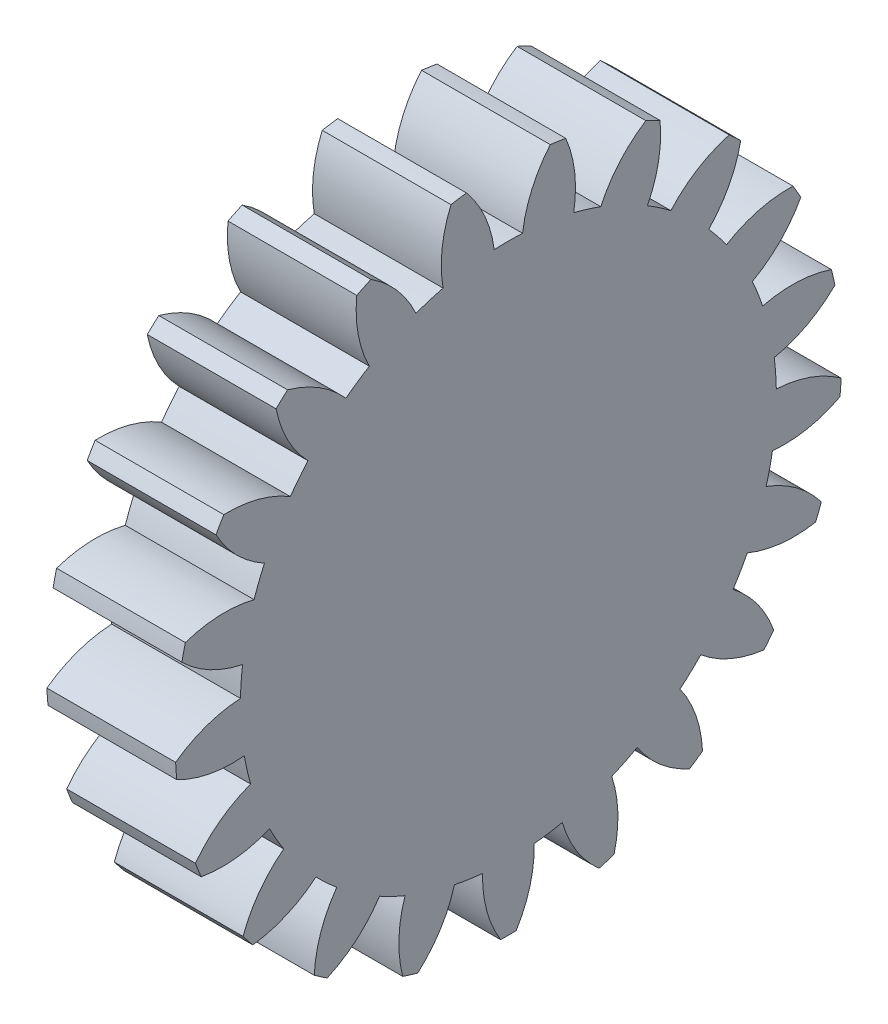
SolidWorks part; units mm, degrees
ref_plane "Plane1" through (0, 0, 0) normal (0, 0, 1) x (1, 0, 0)
ref_plane "Plane2" through (0, 0, 0) normal (0, 1, 0) x (1, 0, 0)
ref_plane "Plane3" through (0, 0, 0) normal (1, 0, 0) x (0, 0, -1)
sketch "HoldingSke" plane through (0, 0, 0) normal (0, 1, 0) x (1, 0, 0)
  line L0 (0, 0) -> (0.4149, -0.1593)
  line L1 (-15, 0) -> (100, 0) construction
  line L2 (0, 0) -> (-2.1039, 2.3779)
  line L3 (0, 0) -> (-11.863, 4.5341)
  line L4 (0, 0) -> (8.0624, 3.0949)
  line L5 (0, 0) -> (-46.8476, -17.4728)
  line L6 (0, 0) -> (-8.2896, -5.593)
  line L7 (-2.1039, 2.3779) -> (8.6586, 51.2059)
  line L8 (-76.2, 54.61) -> (-72.9, 54.61)
  line L9 (-71.009, 38.7566) -> (-53.1078, 45.2721)
  line L10 (-76.2, 71.12) -> (104.1128, 71.12)
  line L11 (0, 0) -> (-10, 0)
  line L12 (-76.2, 101.6) -> (-76.123, 101.6)
  line L13 (24.9733, 27.94) -> (52.9518, 28.4284)
  line L14 (24.9733, 27.94) -> (24.9743, 27.94)
  line L15 (24.9733, 27.94) -> (100.4006, 29.5858)
  line L16 (-63.627, -2.25) -> (-12.827, -2.25)
  circle A0 centre (0, 0) radius 11
  circle A1 centre (0, 0) radius 20.8115
  circle A2 centre (0, 0) radius 37.5
  circle A3 centre (0, 0) radius 11
  dimension "MHD" = 41.623
  dimension "Hub_dia" = 75
  dimension "Bore" = 22
  dimension "MBD" = 22
  dimension "Num_teeth" = 21
  dimension "Pitch" = 0.4444
  dimension "Overall_len" = 50
  dimension "Show_teeth" = 21
  dimension "Thickness" = 10
  dimension "OAL" = 50.0001
  dimension "T_dim" = 3.3
  dimension "Ap" = 20
  dimension "H" = 19.05
  dimension "Pitch_radius" = 180.3128
  dimension "Width" = 10
  dimension "Backlash" = 0.077
  dimension "Addendum_fac" = 1
  dimension "Dedendum_fac" = 1.25
  dimension "Clearance_fac" = 0.25
  dimension "Dedendum_add" = 0.001
  dimension "Module" = 2.25
sketch "BasProSke" plane through (0, 0, 0) normal (0, 1, 0) x (1, 0, 0)
  line L0 (-10, 0) -> (60, 0) construction
  line L1 (0, 0) -> (0, 25.875)
  line L2 (0, 0) -> (10, 0)
  line L3 (10, 0) -> (10, 25.875)
  line L4 (10, 25.875) -> (0, 25.875)
  dimension "Thickness" = 10
  dimension "Diameter" = 51.75
revolve "Base-Revolve" add sketch "BasProSke" angle 360 about L0
sketch "TooCutSke" plane through (0, 0, 0) normal (1, 0, 0) x (0, 0, -1)
  line L1 (0, 0) -> (0, 107) construction
  line L2 (0, 0) -> (-1.9002, 23.5485) construction
  line L3 (0, 0) -> (-7.0255, 46.6108) construction
  line L4 (-1.9002, 23.5485) -> (-3.5127, 23.3054) construction
  arc A0 (1.1014, 20.7823) -> (-1.1014, 20.7823) centre (0, 0) ccw
  arc A1 (3.2722, 25.6929) -> (-3.2722, 25.6929) centre (0, 0) ccw
  circle A2 centre (0, 0) radius 23.625 construction
  circle A3 centre (0, 0) radius 22.2002 construction
  arc A4 (-1.1014, 20.7823) -> (-3.2722, 25.6929) centre (-10.4739, 19.5742) ccw
  arc A5 (3.2722, 25.6929) -> (1.1014, 20.7823) centre (10.4739, 19.5742) ccw
  dimension "Root_dia" = 41.623
  dimension "Overcut_dia" = 51.8008
  dimension "Pitch_dia" = 47.25
  dimension "Base_dia" = 44.4005
  dimension "Flank_rad" = 9.45
  dimension "Half_ang" = 8.571
  dimension "Half_CT" = 1.6307
extrude "ToothCut" cut sketch "TooCutSke" along normal through all
fillet "Breaks" [suppressed] radius 0.045
fillet "RootFillets" [suppressed] radius 0.5635
pattern_circular "TeethCuts" count 21 every 17.143 about axis through (-10, 0, 0) along (1, 0, 0) of "ToothCut", "RootFillets", "Breaks"
sketch "HubNeaOneSke" plane through (0, 0, 0) normal (-1, 0, 0) x (0, 0, 1)
  circle A0 centre (0, 0) radius 20.8115
  dimension "Diameter" = 41.623
extrude "HubNearOne" [suppressed] add sketch "HubNeaOneSke" along normal blind 40.0001
sketch "HubNeaBotSke" plane through (0, 0, 0) normal (-1, 0, 0) x (0, 0, 1)
  circle A0 centre (0, 0) radius 20.8115
  dimension "Diameter" = 41.623
extrude "HubNearBoth" [suppressed] add sketch "HubNeaBotSke" along normal blind 20
ref_plane "FarPln" through (10, 0, 0) normal (1, 0, 0) x (0, 0, -1)
sketch "HubFarSke" plane through (10, 0, 0) normal (1, 0, 0) x (0, 0, -1)
  circle A0 centre (0, 0) radius 20.8115
  dimension "Diameter" = 41.623
extrude "HubFar" [suppressed] add sketch "HubFarSke" along normal blind 20
sketch "BorSke" plane through (0, 0, 0) normal (1, 0, 0) x (0, 0, -1)
  circle A0 centre (0, 0) radius 11
  dimension "Diameter" = 22
extrude "Bore" cut sketch "BorSke" along normal mid plane 100.0001
sketch "KeySke" plane through (0, 0, 0) normal (1, 0, 0) x (0, 0, -1)
  line L0 (-4, 0) -> (-4, 14.3)
  line L1 (-4, 14.3) -> (4, 14.3)
  line L2 (4, 14.3) -> (4, 0)
  line L3 (0, 0) -> (0, 34) construction
  line L4 (-4, 0) -> (4, 0)
  dimension "Offset" = 14.3
  dimension "Width" = 8
extrude "Keyway" [suppressed] cut sketch "KeySke" along normal mid plane 100.0001
pattern_circular "Keyway2" [suppressed] count 2 every 90 about axis through (-10, 0, 0) along (1, 0, 0)
sketch "Sketch1" plane through (10, 0, 0) normal (1, 0, 0) x (0, 0, -1)
  circle A0 centre (0, 0) radius 11 construction
  circle A1 centre (0, 0) radius 11
sketch "Sketch2" plane through (10, 0, 0) normal (1, 0, 0) x (0, 0, -1)
  circle A0 centre (0, 0) radius 11 construction
  circle A1 centre (0, 0) radius 11
extrude "Boss-Extrude2" add sketch "Sketch2" against normal blind 3
equation "' \"Module@HoldingSke\" = 6.35"
equation "' \"Num_teeth@HoldingSke\" = 12"
equation "' \"Ap@HoldingSke\" =  20"
equation "' \"Ap@HoldingSke\" = 20"
equation "' \"Width@HoldingSke\" = 0.5 * 25.4"
equation "' \"Hub_dia@HoldingSke\"= 1 * 25.4"
equation "' \"Hub_dia@HoldingSke\" = 1 * 25.4"
equation "' \"Overall_len@HoldingSke\" = 1.0 * 25.4"
equation "' \"Bore@HoldingSke\" = 0.75 * 25.4"
equation "' \"T_dim@HoldingSke\" = 0.1 * 25.4"
equation "' \"Width@KeySke\" = 0.25 * 25.4"
equation "' \"Show_teeth@HoldingSke\" = 13"
equation "' \"Backlash@HoldingSke\" = 0.009 * 25.4"
equation "' \"Addendum_fac@HoldingSke\" = 1.0"
equation "' \"Dedendum_fac@HoldingSke\" = 1.25"
equation "' \"Dedendum_add@HoldingSke\" = 0.00005 * 25.4"
equation "' \"Clearance_fac@HoldingSke\" = 0.25"
equation "\"Pitch@HoldingSke\" = 1 / \"Module@HoldingSke\""
equation "\"Overcut_dia@TooCutSke\" = (\"Num_teeth@HoldingSke\" + 2 * \"Addendum_fac@HoldingSke\") / \"Pitch@HoldingSke\" + 0.002 * 25.4"
equation "\"Pitch_dia@TooCutSke\" = \"Num_teeth@HoldingSke\" / \"Pitch@HoldingSke\""
equation "\"Base_dia@TooCutSke\" = \"Num_teeth@HoldingSke\" / \"Pitch@HoldingSke\" * cos((\"Ap@HoldingSke\"  * 3.14159265 / 180))"
equation "\"Root_dia@TooCutSke\" = (\"Num_teeth@HoldingSke\" + 2) / \"Pitch@HoldingSke\" - 2 * (\"Addendum_fac@HoldingSke\" + \"Dedendum_fac@HoldingSke\") / \"Pitch@HoldingSke\" - \"Dedendum_add@HoldingSke\" * 2"
equation "\"Half_ang@TooCutSke\" = 180 / \"Num_teeth@HoldingSke\""
equation "\"Half_CT@TooCutSke\" = \"Num_teeth@HoldingSke\" / \"Pitch@HoldingSke\" * sin((3.14159265 / 2 / \"Num_teeth@HoldingSke\")) / 2 - 7 * \"Backlash@HoldingSke\" / 4"
equation "\"Flank_rad@TooCutSke\" = \"Num_teeth@HoldingSke\" / \"Pitch@HoldingSke\" / 5"
equation "\"Radius@RootFillets\" = \"Clearance_fac@HoldingSke\" / \"Pitch@HoldingSke\" + \"Dedendum_add@HoldingSke\""
equation "\"Break_rad@Breaks\" = 0.02 / \"Pitch@HoldingSke\""
equation "\"Thickness@HoldingSke\" = \"Width@HoldingSke\""
equation "\"OAL@HoldingSke\" = \"Thickness@HoldingSke\""
equation "\"MHD@HoldingSke\" = (\"Num_teeth@HoldingSke\" + 2) / \"Pitch@HoldingSke\" - 2 * (\"Addendum_fac@HoldingSke\" + \"Dedendum_fac@HoldingSke\")  / \"Pitch@HoldingSke\" - \"Dedendum_add@HoldingSke\" * 2"
equation "\"MBD@HoldingSke\" = (\"Num_teeth@HoldingSke\" + 2) / \"Pitch@HoldingSke\" - 2 * (\"Addendum_fac@HoldingSke\" + \"Dedendum_fac@HoldingSke\")  / \"Pitch@HoldingSke\" - \"Dedendum_add@HoldingSke\" * 2 - 0.002 * 25.4"
equation "\"MHD@HoldingSke\" = ((sgn( \"MHD@HoldingSke\" - \"Hub_dia@HoldingSke\" )-1)*( \"MHD@HoldingSke\" - \"Hub_dia@HoldingSke\" ))/-2+ \"Hub_dia@HoldingSke\""
equation "\"MBD@HoldingSke\" = ((sgn( \"MBD@HoldingSke\" - \"Bore@HoldingSke\" )-1)*( \"MBD@HoldingSke\" - \"Bore@HoldingSke\" ))/-2+ \"Bore@HoldingSke\""
equation "\"OAL@HoldingSke\" = ((sgn( \"OAL@HoldingSke\" - \"Overall_len@HoldingSke\" )+1)*( \"OAL@HoldingSke\" - \"Overall_len@HoldingSke\" ))/2 + \"Overall_len@HoldingSke\" + 0.000002 * 25.4"
equation "\"Num_teeth@TeethCuts\" = int( \"Show_teeth@HoldingSke\" ) + 1"
equation "\"Num_teeth@TeethCuts\" = ((sgn( \"Num_teeth@TeethCuts\" - \"Num_teeth@HoldingSke\" )-1)*( \"Num_teeth@TeethCuts\" - \"Num_teeth@HoldingSke\" ))/-2+ \"Num_teeth@HoldingSke\""
equation "\"Num_teeth@TeethCuts\" = ((sgn( \"Num_teeth@TeethCuts\" - 2.0)+1)*( \"Num_teeth@TeethCuts\" - 2.0))/2 +2.0"
equation "\"Angle@TeethCuts\" = 360.0 / \"Num_teeth@HoldingSke\""
equation "\"Diameter@BasProSke\" = (\"Num_teeth@HoldingSke\" + 2 * \"Addendum_fac@HoldingSke\") / \"Pitch@HoldingSke\""
equation "\"Thickness@BasProSke\"  = \"Thickness@HoldingSke\""
equation "' \"Fillet_rad@BasProSke\" =  \"Thickness@HoldingSke\" * 0.05"
equation "' \"Fillet_rad@BasProSke\" = \"Thickness@HoldingSke\" * 0.05"
equation "\"MHD@HoldingSke\" = ((sgn( \"MHD@HoldingSke\" - \"Root_dia@TooCutSke\" )-1)*( \"MHD@HoldingSke\" - \"Root_dia@TooCutSke\" ))/-2+ \"Root_dia@TooCutSke\""
equation "\"Diameter@HubNeaOneSke\" = \"MHD@HoldingSke\""
equation "\"Length@HubNearOne\" = \"OAL@HoldingSke\" - \"Thickness@BasProSke\""
equation "\"Diameter@HubNeaBotSke\" = \"MHD@HoldingSke\""
equation "\"Length@HubNearBoth\" = ( \"OAL@HoldingSke\" - \"Thickness@BasProSke\" ) / 2.0"
equation "\"Thickness@FarPln\" = \"Thickness@BasProSke\""
equation "\"Diameter@HubFarSke\" = \"MHD@HoldingSke\""
equation "\"Length@HubFar\" = ( \"OAL@HoldingSke\" - \"Thickness@BasProSke\" ) / 2.0"
equation "\"Diameter@BorSke\" = \"MBD@HoldingSke\""
equation "\"D1@Bore\" = \"OAL@HoldingSke\" * 2.0"
equation "\"D1@Keyway\" = \"OAL@HoldingSke\" * 2.0"
equation "\"Offset@KeySke\" = \"T_dim@HoldingSke\" + \"MBD@HoldingSke\" / 2.0"
